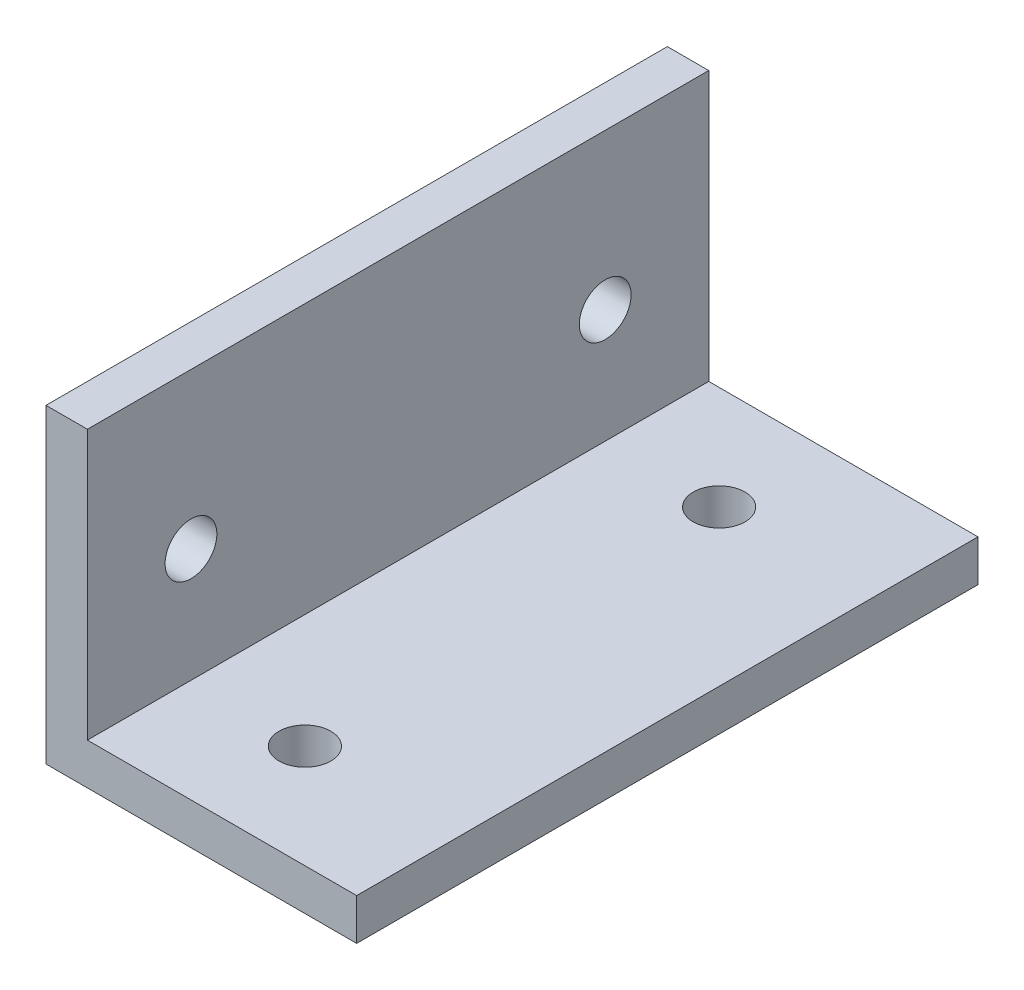
SolidWorks part; units mm, degrees
ref_plane "正面" through (0, 0, 0) normal (0, 0, 1) x (1, 0, 0)
ref_plane "平面" through (0, 0, 0) normal (0, 1, 0) x (1, 0, 0)
ref_plane "右側面" through (0, 0, 0) normal (1, 0, 0) x (0, 0, -1)
sketch "ｽｹｯﾁ1" plane through (0, 0, 0) normal (0, 0, 1) x (1, 0, 0)
  line L0 (0, 0) -> (0, 15)
  line L1 (0, 15) -> (2, 15)
  line L2 (2, 15) -> (2, 2)
  line L3 (2, 2) -> (15, 2)
  line L4 (15, 2) -> (15, 0)
  line L5 (15, 0) -> (0, 0)
  dimension "D1" = 2
  dimension "D2" = 2
  dimension "D3" = 15
  dimension "D4" = 15
  dimension "D5" = 13
  dimension "D6" = 13
extrude "ﾎﾞｽ - 押し出し1" add sketch "ｽｹｯﾁ1" along normal blind 30
sketch "ｽｹｯﾁ2" plane through (0, 0, 0) normal (-1, 0, 0) x (0, 0, 1)
  line L0 (0, 7.5) -> (5, 7.5)
  line L1 (0, 15) -> (0, 0) construction
  line L2 (5, 7.5) -> (25, 7.5)
  circle A0 centre (5, 7.5) radius 1.6
  circle A1 centre (25, 7.5) radius 1.6
  dimension "D3" = 3.2
  dimension "D4" = 3.2
  dimension "D1" = 5
  dimension "D2" = 20
sketch "ｽｹｯﾁ4" plane through (0, 0, 0) normal (0, -1, 0) x (-1, 0, 0)
  line L0 (-7.5, 0) -> (-7.5, -5)
  line L1 (0, 0) -> (-15, 0) construction
  line L2 (-7.5, -5) -> (-7.5, -25)
  circle A0 centre (-7.5, -5) radius 1.6
  circle A1 centre (-7.5, -25) radius 1.6
  dimension "D1" = 3.2
  dimension "D2" = 3.2
  dimension "D3" = 5
  dimension "D4" = 20
hole_wizard "M3x0.5 ねじ穴1" positions "3Dｽｹｯﾁ1" profile "ｽｹｯﾁ5" tap size "M3x0.5" standard "JIS"
sketch3d "3Dｽｹｯﾁ1"
  point P0 (7.5, 0, 5)
  point P3 (7.5, 0, 25)
  point P6 (0, 7.5, 25)
  point P9 (0, 7.5, 5)
sketch "ｽｹｯﾁ5" plane through (7.5, 0, 5) normal (1, 0, 0) x (0, 0, -1)
  line L0 (0, 0) -> (0, 9.2511)
  line L1 (0, 9.2511) -> (1.25, 8.5)
  line L2 (1.25, 8.5) -> (1.25, 0)
  line L5 (1.25, 0) -> (0, 0)
  line L10 (0, 9.2511) -> (-1.25, 8.5) construction
  line L11 (0, -6.35) -> (0, 107.95) construction
  dimension "ねじ下穴ﾄﾞﾘﾙ直径" = 2.5
  dimension "ねじ下穴ﾄﾞﾘﾙの深さ" = 8.5
  dimension "ﾄﾞﾘﾙ角度" = 118
cosmetic thread "穴のねじ山1" parameters "D1"=2, "D2"=3
cosmetic thread "穴のねじ山2" parameters "D1"=2, "D2"=3
cosmetic thread "穴のねじ山3" parameters "D1"=2, "D2"=3
cosmetic thread "穴のねじ山4" parameters "D1"=2, "D2"=3
